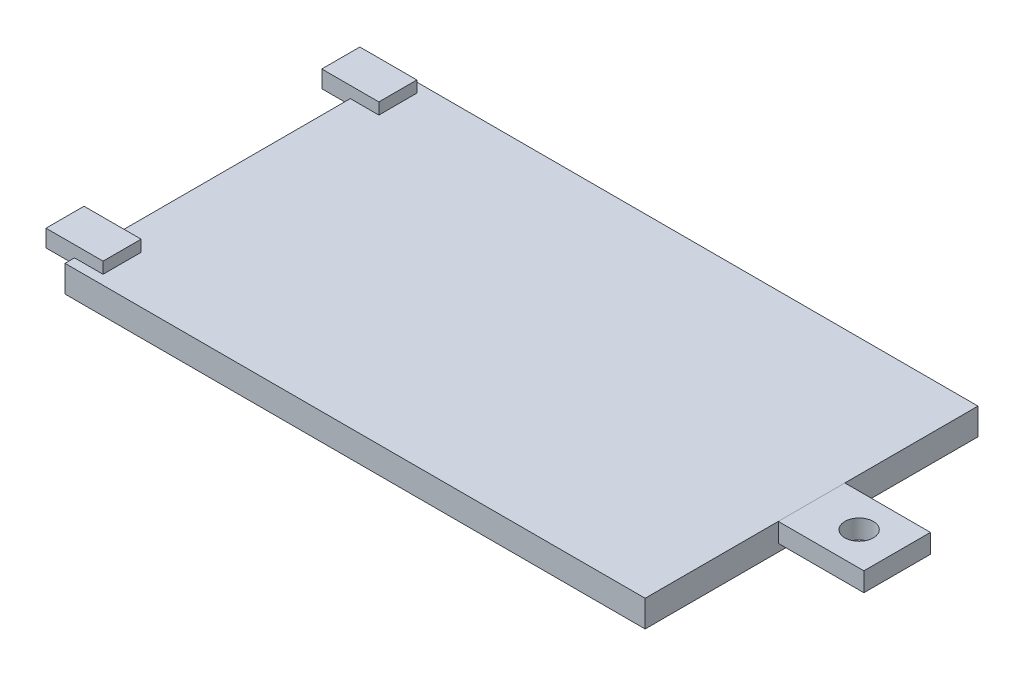
SolidWorks part; units mm, degrees
ref_plane "前视基准面" through (0, 0, 0) normal (0, 0, 1) x (1, 0, 0)
ref_plane "上视基准面" through (0, 0, 0) normal (0, 1, 0) x (1, 0, 0)
ref_plane "右视基准面" through (0, 0, 0) normal (1, 0, 0) x (0, 0, -1)
sketch "草图1" plane through (0, 0, 0) normal (0, 1, 0) x (1, 0, 0)
  line L1 (0, 0) -> (61, 0)
  line L2 (0, 0) -> (0, 35)
  line L3 (0, 35) -> (61, 35)
  line L4 (61, 0) -> (61, 35)
  dimension "D1" = 35
  dimension "D2" = 61
extrude "凸台-拉伸1" add sketch "草图1" along normal blind 2.8
sketch "草图2" plane through (0, 2.8, 0) normal (0, -1, 0) x (1, 0, 0)
  line L0 (61, 0) -> (61, -35) construction
  line L1 (61, -21) -> (70, -21)
  line L2 (61, -21) -> (61, -14)
  line L3 (61, -14) -> (70, -14)
  line L4 (70, -21) -> (70, -14)
  line L5 (61, -17.5) -> (70.5631, -17.5) construction
  line L6 (61, -17.5) -> (69.0513, -17.5) construction
  circle A0 centre (66, -17.5) radius 1.5
  dimension "D3" = 3
  dimension "D1" = 7
  dimension "D2" = 9
  dimension "D4" = 4
extrude "凸台-拉伸2" add sketch "草图2" along normal blind 2 separate body
sketch "草图3" plane through (0, 0, 0) normal (-1, 0, 0) x (0, 0, 1)
  line L0 (-35, 2.8) -> (0, 2.8) construction
  line L1 (-5, 4) -> (-1, 4)
  line L2 (-5, 4) -> (-5, 2.2)
  line L3 (-5, 2.2) -> (-1, 2.2)
  line L4 (-1, 4) -> (-1, 2.2)
  line L5 (0, 2.8) -> (0, 0) construction
  line L6 (-17.5, 0) -> (-17.5, 11.6055) construction
  line L7 (-35, 0) -> (0, 0) construction
  line L8 (-30, 2.2) -> (-34, 2.2)
  line L9 (-34, 4) -> (-34, 2.2)
  line L10 (-30, 4) -> (-34, 4)
  line L11 (-30, 4) -> (-30, 2.2)
  dimension "D1" = 4
  dimension "D2" = 0.6
  dimension "D3" = 1.2
  dimension "D4" = 1
extrude "凸台-拉伸3" add sketch "草图3" along normal mid plane 6
